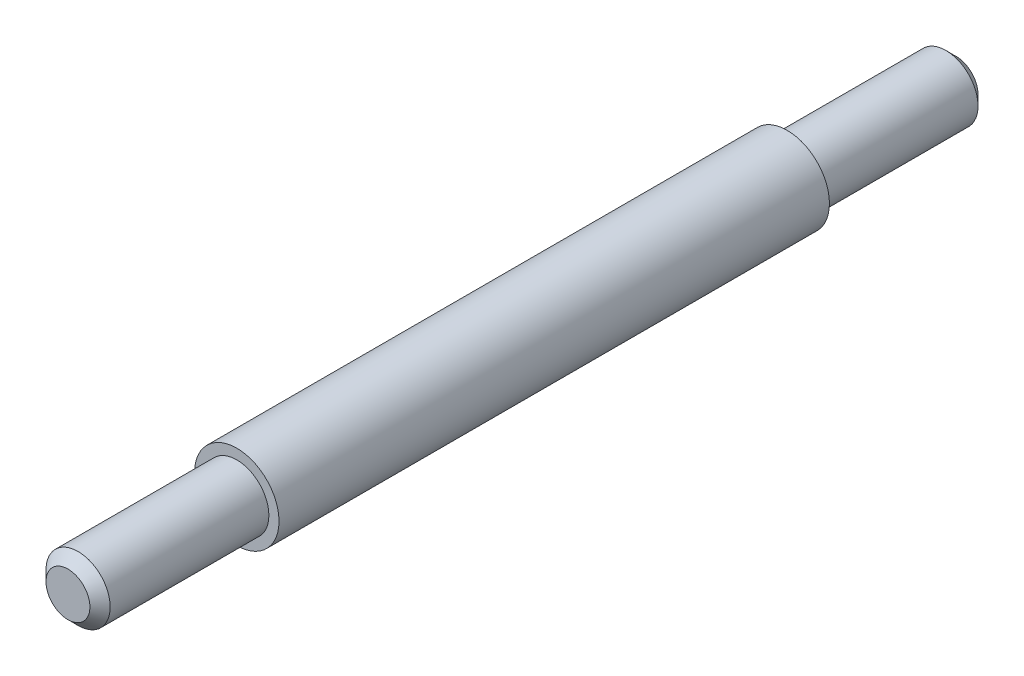
SolidWorks part; units mm, degrees
ref_plane "Front Plane" through (0, 0, 0) normal (0, 0, 1) x (1, 0, 0)
ref_plane "Top Plane" through (0, 0, 0) normal (0, 1, 0) x (1, 0, 0)
ref_plane "Right Plane" through (0, 0, 0) normal (1, 0, 0) x (0, 0, -1)
sketch "Sketch2" plane through (0, 0, 0) normal (0, 1, 0) x (1, 0, 0)
  line L0 (0, 0) -> (0.095, 0)
  line L1 (0.095, 0) -> (0.095, 0.5)
  line L2 (0.095, 0.5) -> (0.125, 0.5)
  line L3 (0.125, 0.5) -> (0.125, 2.13)
  line L4 (0.125, 2.13) -> (0.095, 2.13)
  line L5 (0.095, 2.13) -> (0.095, 2.63)
  line L6 (0.095, 2.63) -> (0, 2.63)
  line L7 (0, 0) -> (0, 2.63) construction
  line L8 (0, 0) -> (0, 2.63)
  point P3 (0, 0)
  point P10 (0, 0)
  dimension "D1" = 0.095
  dimension "D2" = 0.125
  dimension "D3" = 0.5
  dimension "D4" = 1.63
  dimension "D5" = 2.63
revolve "Revolve1" add sketch "Sketch2" angle 360 about L7
chamfer "Chamfer1" distance 0.03 2 edges at (0.095, 0, -2.63) (0.095, 0, 0)
